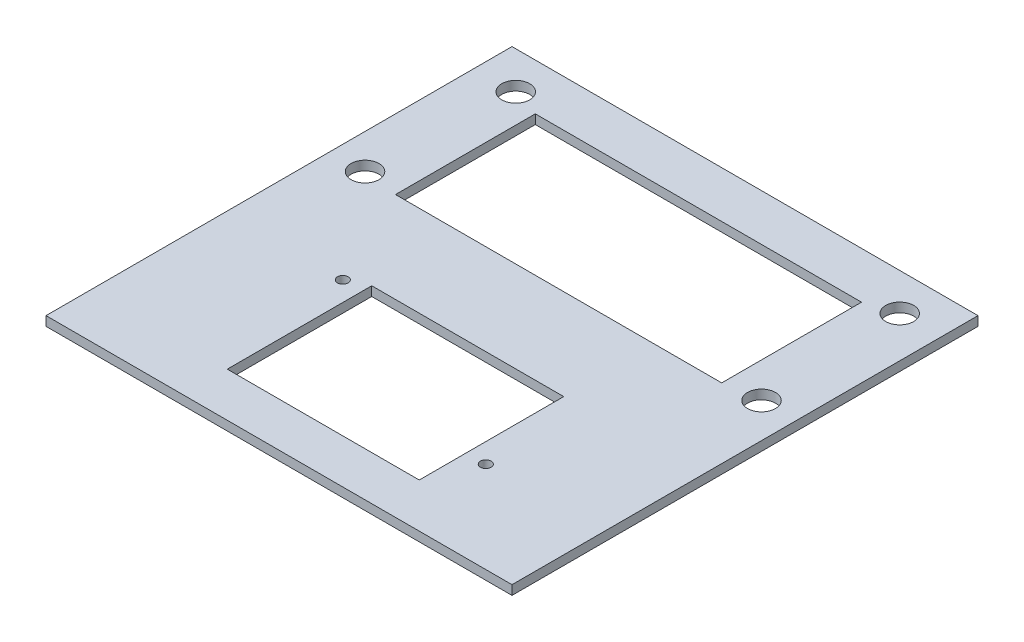
SolidWorks part; units mm, degrees
ref_plane "Front" through (0, 0, 0) normal (0, 0, 1) x (1, 0, 0)
ref_plane "Top" through (0, 0, 0) normal (0, 1, 0) x (1, 0, 0)
ref_plane "Right" through (0, 0, 0) normal (1, 0, 0) x (0, 0, -1)
sketch "Sketch1" plane through (0, 0, 0) normal (0, 1, 0) x (1, 0, 0)
  line L1 (31.75, -31.75) -> (-31.75, -31.75)
  line L2 (31.75, -31.75) -> (31.75, 31.75)
  line L3 (31.75, 31.75) -> (-31.75, 31.75)
  line L4 (-31.75, -31.75) -> (-31.75, 31.75)
  line L5 (31.75, -31.75) -> (-31.75, 31.75) construction
  line L6 (31.75, 31.75) -> (-31.75, -31.75) construction
  point P0 (0, 0)
  dimension "D1" = 63.5
  dimension "D2" = 63.5
extrude "Boss-Extrude1" add sketch "Sketch1" along normal blind 1.27
sketch "Sketch2" plane through (0, 1.27, 0) normal (0, 1, 0) x (1, 0, 0)
  line L0 (0, 31.75) -> (0, -31.75) construction
  line L1 (31.75, 31.75) -> (-31.75, 31.75) construction
  line L2 (-31.75, -31.75) -> (31.75, -31.75) construction
  line L3 (-31.75, 0) -> (31.75, 0) construction
  line L4 (-31.75, 31.75) -> (-31.75, -31.75) construction
  line L5 (31.75, -31.75) -> (31.75, 31.75) construction
  line L6 (-31.75, 31.75) -> (-31.75, 0) construction
  line L7 (-31.75, 15.875) -> (31.75, 15.875) construction
  line L8 (-26.162, 26.67) -> (-26.162, 31.75)
  line L9 (-26.162, 26.67) -> (-31.75, 26.67)
  line L10 (-27.0129, 6.985) -> (-31.75, 6.985)
  line L11 (-27.0129, 6.985) -> (-27.0129, 31.75)
  circle A0 centre (-26.162, 26.67) radius 1.905
  circle A1 centre (-27.0129, 6.985) radius 1.905
  circle A2 centre (27.0129, 6.985) radius 1.905
  circle A3 centre (26.162, 26.67) radius 1.905
  point P16 (0, 15.875)
  point P17 (0, 0)
  dimension "D1" = 3.81
  dimension "D4" = 3.81
  dimension "D2" = 5.588
  dimension "D3" = 5.08
  dimension "D5" = 24.765
  dimension "D6" = 4.7371
extrude "Cut-Extrude1" cut sketch "Sketch2" against normal blind 1.27 contours A2 | A3 | A1 | A0
sketch "Sketch3" plane through (0, 1.27, 0) normal (0, 1, 0) x (1, 0, 0)
  line L0 (0, 31.75) -> (0, 0) construction
  line L1 (31.75, 31.75) -> (-31.75, 31.75) construction
  line L2 (-31.75, 0) -> (31.75, 0) construction
  line L3 (-31.75, 31.75) -> (-31.75, -31.75) construction
  line L4 (31.75, -31.75) -> (31.75, 31.75) construction
  line L5 (-31.75, 0) -> (-31.75, 31.75) construction
  line L6 (31.75, 0) -> (31.75, 31.75) construction
  line L7 (-31.75, 15.875) -> (31.75, 15.875) construction
  line L9 (22.225, 6.35) -> (-22.225, 6.35)
  line L10 (22.225, 6.35) -> (22.225, 25.4)
  line L11 (22.225, 25.4) -> (-22.225, 25.4)
  line L12 (-22.225, 6.35) -> (-22.225, 25.4)
  line L13 (22.225, 6.35) -> (-22.225, 25.4) construction
  line L14 (22.225, 25.4) -> (-22.225, 6.35) construction
  point P17 (0, 15.875)
  dimension "D1" = 44.45
  dimension "D2" = 19.05
extrude "Cut-Extrude2" cut sketch "Sketch3" against normal blind 1.27
sketch "Sketch4" plane through (0, 1.27, 0) normal (0, 1, 0) x (1, 0, 0)
  line L0 (-31.75, 0) -> (31.75, 0) construction
  line L1 (-31.75, 31.75) -> (-31.75, -31.75) construction
  line L2 (31.75, -31.75) -> (31.75, 31.75) construction
  line L3 (0, 0) -> (0, -31.75) construction
  line L4 (-31.75, -31.75) -> (31.75, -31.75) construction
  line L5 (0, -15.875) -> (-31.75, -15.875) construction
  line L6 (-31.75, -15.875) -> (31.75, -15.875) construction
  line L7 (-15.748, -6.0325) -> (-15.748, -7.3025) construction
  line L12 (16.7894, -25.7175) -> (-16.7894, -6.0325) construction
  line L13 (16.7894, -6.0325) -> (-16.7894, -25.7175) construction
  line L14 (-15.748, -7.3025) -> (-16.7894, -7.3025) construction
  line L15 (15.748, -6.0325) -> (15.748, -19.3167) construction
  line L16 (15.748, -19.3167) -> (16.7894, -19.3167) construction
  circle A0 centre (-15.748, -7.3025) radius 0.7302
  circle A1 centre (15.748, -19.3167) radius 0.7303
  dimension "D7" = 1.4605
  dimension "D8" = 1.4605
  dimension "D1" = 19.685
  dimension "D2" = 33.5788
  dimension "D3" = 1.27
  dimension "D4" = 1.0414
  dimension "D5" = 13.2842
  dimension "D6" = 1.0414
extrude "Boss-Extrude2" add sketch "Sketch4" against normal blind 3.81
sketch "Sketch5" plane through (0, 1.27, 0) normal (0, 1, 0) x (1, 0, 0)
  line L1 (13.081, -25.7175) -> (-13.081, -25.7175)
  line L3 (13.081, -25.7175) -> (13.081, -6.0325)
  line L4 (0, 0) -> (0, -31.75) construction
  line L5 (13.081, -6.0325) -> (-13.081, -6.0325)
  line L6 (-13.081, -25.7175) -> (-13.081, -6.0325)
  line L7 (13.081, -25.7175) -> (-13.081, -6.0325) construction
  line L8 (13.081, -6.0325) -> (-13.081, -25.7175) construction
  point P0 (0, -15.875)
  dimension "D1" = 26.162
  dimension "D2" = 19.685
extrude "Cut-Extrude3" cut sketch "Sketch5" against normal up to next
sketch "Sketch6" plane through (0, -2.54, 0) normal (0, -1, 0) x (1, 0, 0)
  circle A0 centre (15.748, 19.3167) radius 0.7303
  circle A1 centre (-15.748, 7.3025) radius 0.7302
extrude "Cut-Extrude4" cut sketch "Sketch6" against normal through all
